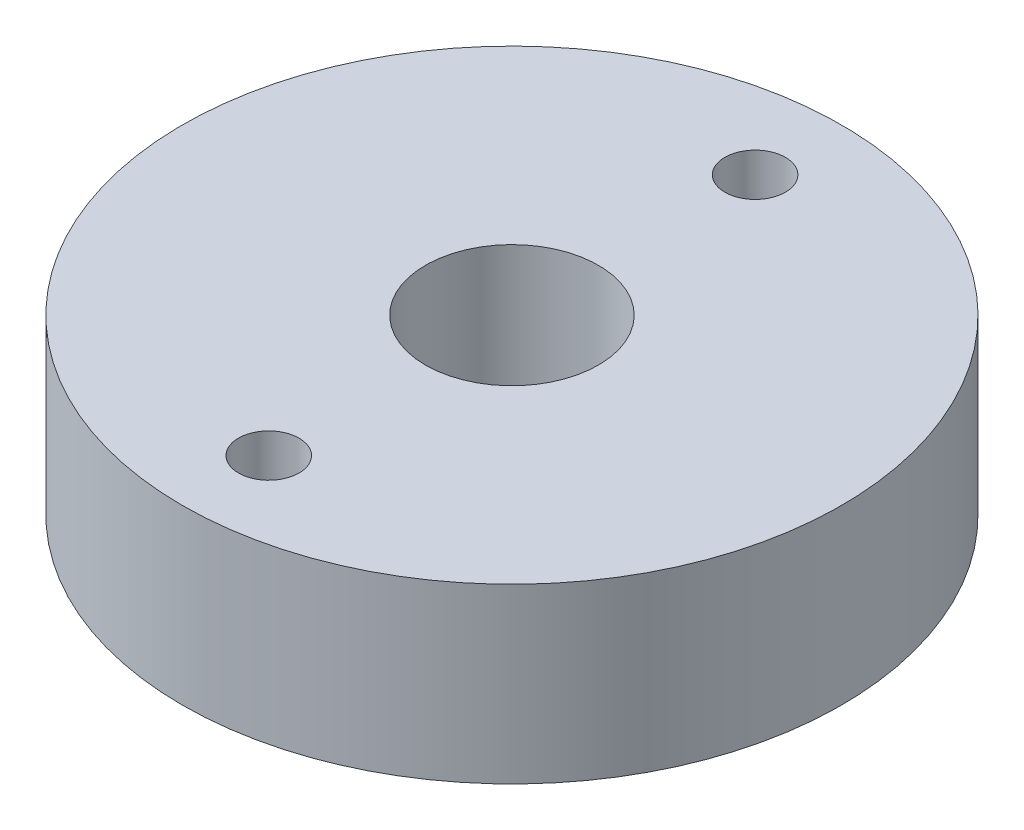
SolidWorks part; units mm, degrees
ref_plane "Front Plane" through (0, 0, 0) normal (0, 0, 1) x (1, 0, 0)
ref_plane "Top Plane" through (0, 0, 0) normal (0, 1, 0) x (1, 0, 0)
ref_plane "Right Plane" through (0, 0, 0) normal (1, 0, 0) x (0, 0, -1)
sketch "Sketch1" plane through (0, 0, 0) normal (0, 1, 0) x (1, 0, 0)
  circle A0 centre (0, 0) radius 5
  circle A1 centre (0, 0) radius 19.055
  circle A2 centre (0, -14.06) radius 1.75
  circle A3 centre (0, 14.06) radius 1.75
  point P10 (0, 0)
  dimension "D2" = 38.11
  dimension "D3" = 10
  dimension "D4" = 3.5
  dimension "D1" = 14.06
  dimension "D5" = 2
extrude "Boss-Extrude1" add sketch "Sketch1" along normal blind 10
